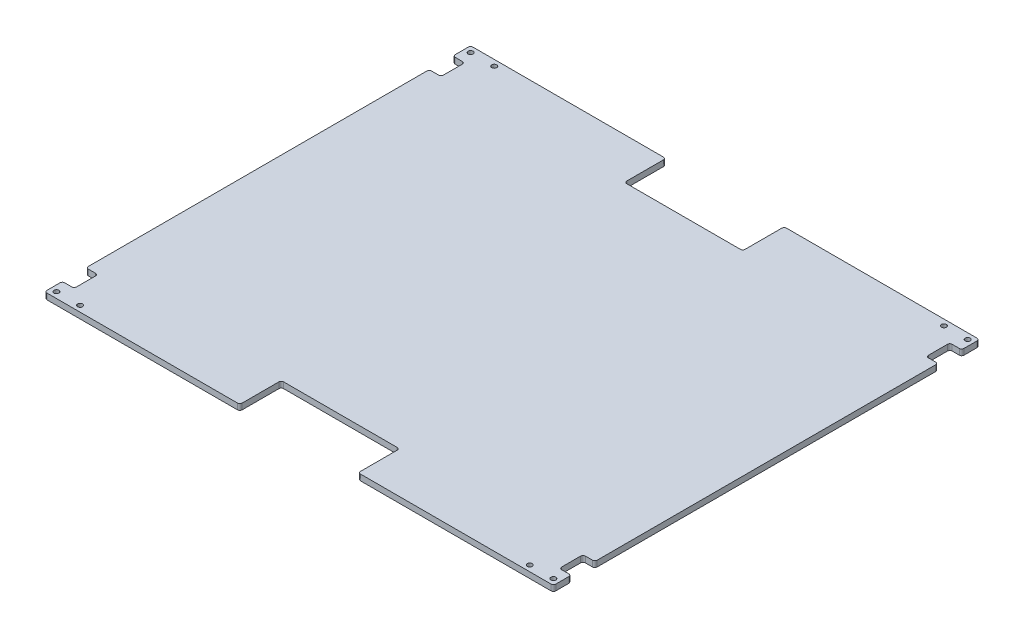
SolidWorks part; units mm, degrees
ref_plane "Front Plane" through (0, 0, 0) normal (0, 0, 1) x (1, 0, 0)
ref_plane "Top Plane" through (0, 0, 0) normal (0, 1, 0) x (1, 0, 0)
ref_plane "Right Plane" through (0, 0, 0) normal (1, 0, 0) x (0, 0, -1)
sketch "Sketch1" plane through (0, 0, 0) normal (0, 1, 0) x (1, 0, 0)
  line L0 (-273.05, 226.06) -> (-273.05, 212.09)
  line L1 (273.05, 226.06) -> (273.05, 212.09)
  line L2 (270.51, 228.6) -> (66.04, 228.6)
  line L3 (-270.51, -228.6) -> (-66.04, -228.6)
  line L4 (-270.51, 209.55) -> (-262.89, 209.55)
  line L5 (-260.35, 207.01) -> (-260.35, 186.69)
  line L6 (-262.89, 184.15) -> (-270.51, 184.15)
  line L7 (-273.05, 181.61) -> (-273.05, -181.61)
  line L8 (0, -55) -> (0, 55) construction
  line L9 (262.89, 184.15) -> (270.51, 184.15)
  line L10 (260.35, 207.01) -> (260.35, 186.69)
  line L11 (270.51, 209.55) -> (262.89, 209.55)
  line L12 (273.05, 181.61) -> (273.05, -181.61)
  line L13 (273.05, 0) -> (-273.05, 0) construction
  line L14 (270.51, -209.55) -> (262.89, -209.55)
  line L15 (262.89, -184.15) -> (270.51, -184.15)
  line L16 (260.35, -207.01) -> (260.35, -186.69)
  line L17 (-260.35, -207.01) -> (-260.35, -186.69)
  line L18 (-270.51, -209.55) -> (-262.89, -209.55)
  line L19 (-262.89, -184.15) -> (-270.51, -184.15)
  line L20 (-273.05, -212.09) -> (-273.05, -226.06)
  line L21 (273.05, -212.09) -> (273.05, -226.06)
  line L22 (63.5, 226.06) -> (63.5, 186.69)
  line L23 (60.96, 184.15) -> (-60.96, 184.15)
  line L24 (-63.5, 186.69) -> (-63.5, 226.06)
  line L25 (-66.04, 228.6) -> (-270.51, 228.6)
  line L26 (-63.5, -186.69) -> (-63.5, -226.06)
  line L27 (60.96, -184.15) -> (-60.96, -184.15)
  line L28 (63.5, -226.06) -> (63.5, -186.69)
  line L29 (66.04, -228.6) -> (270.51, -228.6)
  circle A0 centre (-266.7, 222.25) radius 2.667
  circle A1 centre (266.7, 222.25) radius 2.667
  circle A2 centre (-241.3, 222.25) radius 2.667
  circle A3 centre (241.3, 222.25) radius 2.667
  circle A4 centre (-266.7, -222.25) radius 2.667
  circle A5 centre (266.7, -222.25) radius 2.667
  circle A6 centre (-241.3, -222.25) radius 2.667
  circle A7 centre (241.3, -222.25) radius 2.667
  arc A8 (-273.05, -226.06) -> (-270.51, -228.6) centre (-270.51, -226.06) ccw
  arc A9 (273.05, -226.06) -> (270.51, -228.6) centre (270.51, -226.06) cw
  arc A10 (-273.05, 226.06) -> (-270.51, 228.6) centre (-270.51, 226.06) cw
  arc A11 (273.05, 226.06) -> (270.51, 228.6) centre (270.51, 226.06) ccw
  arc A12 (270.51, 209.55) -> (273.05, 212.09) centre (270.51, 212.09) ccw
  arc A13 (260.35, 207.01) -> (262.89, 209.55) centre (262.89, 207.01) cw
  arc A14 (270.51, 184.15) -> (273.05, 181.61) centre (270.51, 181.61) cw
  arc A15 (262.89, 184.15) -> (260.35, 186.69) centre (262.89, 186.69) cw
  arc A16 (270.51, -184.15) -> (273.05, -181.61) centre (270.51, -181.61) ccw
  arc A17 (262.89, -184.15) -> (260.35, -186.69) centre (262.89, -186.69) ccw
  arc A18 (262.89, -209.55) -> (260.35, -207.01) centre (262.89, -207.01) cw
  arc A19 (270.51, -209.55) -> (273.05, -212.09) centre (270.51, -212.09) cw
  arc A20 (-270.51, -184.15) -> (-273.05, -181.61) centre (-270.51, -181.61) cw
  arc A21 (-270.51, -209.55) -> (-273.05, -212.09) centre (-270.51, -212.09) ccw
  arc A22 (-260.35, -186.69) -> (-262.89, -184.15) centre (-262.89, -186.69) ccw
  arc A23 (-260.35, -207.01) -> (-262.89, -209.55) centre (-262.89, -207.01) cw
  arc A24 (-260.35, 186.69) -> (-262.89, 184.15) centre (-262.89, 186.69) cw
  arc A25 (-273.05, 181.61) -> (-270.51, 184.15) centre (-270.51, 181.61) cw
  arc A26 (-260.35, 207.01) -> (-262.89, 209.55) centre (-262.89, 207.01) ccw
  arc A27 (-273.05, 212.09) -> (-270.51, 209.55) centre (-270.51, 212.09) ccw
  arc A28 (-63.5, 226.06) -> (-66.04, 228.6) centre (-66.04, 226.06) ccw
  arc A29 (63.5, 186.69) -> (60.96, 184.15) centre (60.96, 186.69) cw
  arc A30 (63.5, 226.06) -> (66.04, 228.6) centre (66.04, 226.06) cw
  arc A31 (-60.96, 184.15) -> (-63.5, 186.69) centre (-60.96, 186.69) cw
  arc A32 (-60.96, -184.15) -> (-63.5, -186.69) centre (-60.96, -186.69) ccw
  arc A33 (63.5, -226.06) -> (66.04, -228.6) centre (66.04, -226.06) ccw
  arc A34 (63.5, -186.69) -> (60.96, -184.15) centre (60.96, -186.69) ccw
  arc A35 (-63.5, -226.06) -> (-66.04, -228.6) centre (-66.04, -226.06) cw
  point P44 (-273.05, -228.6)
  point P47 (273.05, -228.6)
  point P50 (-273.05, 228.6)
  point P55 (273.05, 209.55)
  point P58 (260.35, 209.55)
  point P61 (273.05, 184.15)
  point P64 (260.35, 184.15)
  point P67 (273.05, -184.15)
  point P70 (260.35, -184.15)
  point P73 (260.35, -209.55)
  point P76 (273.05, -209.55)
  point P79 (-273.05, -184.15)
  point P82 (-273.05, -209.55)
  point P85 (-260.35, -184.15)
  point P88 (-260.35, -209.55)
  point P91 (-260.35, 184.15)
  point P94 (-273.05, 184.15)
  point P97 (-260.35, 209.55)
  point P100 (-273.05, 209.55)
  point P104 (0, 0)
  point P107 (-63.5, 228.6)
  point P110 (63.5, 184.15)
  point P113 (63.5, 228.6)
  point P116 (-63.5, 184.15)
  point P129 (-63.5, -184.15)
  point P130 (63.5, -228.6)
  point P131 (63.5, -184.15)
  point P132 (-63.5, -228.6)
  dimension "D1" = 533.4
  dimension "D3" = 5.334
  dimension "D4" = 25.4
  dimension "D5" = 25.4
  dimension "D8" = 533.4
  dimension "D9" = 6.35
  dimension "D10" = 6.35
  dimension "D11" = 444.5
  dimension "D14" = 5.334
  dimension "D19" = 2.54
  dimension "D23" = 2.54
  dimension "D2" = 457.2
  dimension "D6" = 25.4
  dimension "D7" = 25.4
  dimension "D12" = 6.35
  dimension "D13" = 6.35
  dimension "D15" = 19.05
  dimension "D16" = 12.7
  dimension "D17" = 25.4
  dimension "D18" = 228.6
  dimension "D20" = 127
  dimension "D21" = 63.5
  dimension "D22" = 44.45
  dimension "D24" = 2.54
extrude "Boss-Extrude1" add sketch "Sketch1" along normal blind 6.35
